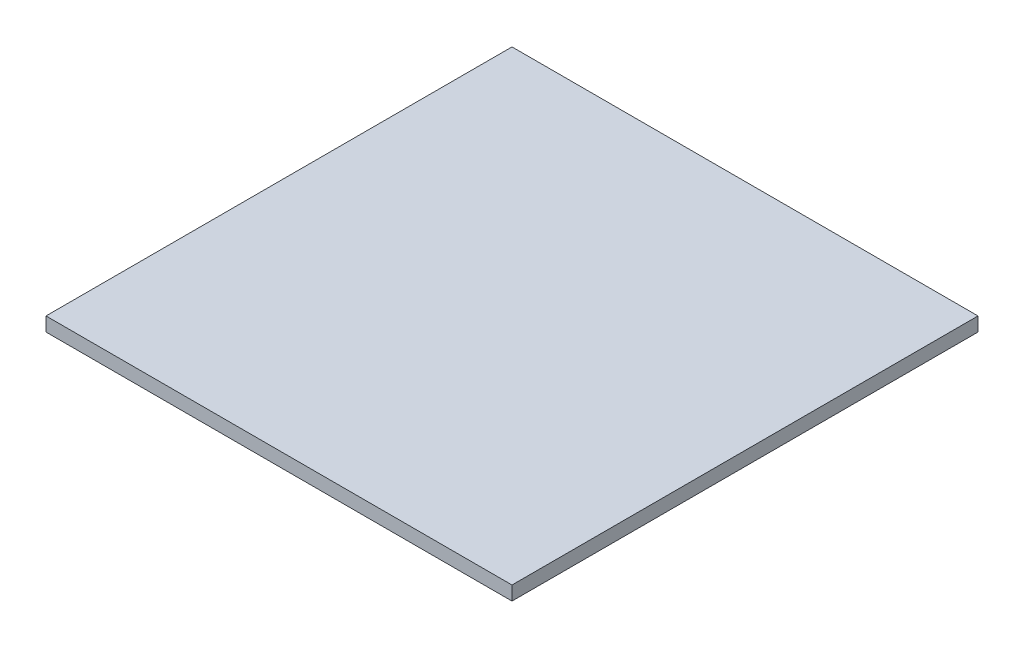
SolidWorks part; units mm, degrees
ref_plane "Front Plane" through (0, 0, 0) normal (0, 0, 1) x (1, 0, 0)
ref_plane "Top Plane" through (0, 0, 0) normal (0, 1, 0) x (1, 0, 0)
ref_plane "Right Plane" through (0, 0, 0) normal (1, 0, 0) x (0, 0, -1)
sketch "Sketch1" plane through (0, 0, 0) normal (0, 1, 0) x (1, 0, 0)
  line L0 (-29.6545, 29.6545) -> (29.6545, 29.6545)
  line L1 (-30.2895, -30.2895) -> (30.2895, -30.2895) construction
  line L2 (-30.2895, -30.2895) -> (-30.2895, 30.2895) construction
  line L3 (-30.2895, 30.2895) -> (30.2895, 30.2895) construction
  line L4 (30.2895, -30.2895) -> (30.2895, 30.2895) construction
  line L5 (-30.2895, -30.2895) -> (30.2895, 30.2895) construction
  line L6 (-30.2895, 30.2895) -> (30.2895, -30.2895) construction
  line L7 (29.6545, -29.6545) -> (29.6545, 29.6545)
  line L8 (-29.6545, -29.6545) -> (29.6545, -29.6545)
  line L9 (-29.6545, -29.6545) -> (-29.6545, 29.6545)
  point P0 (0, 0)
  dimension "D1" = 60.579
  dimension "D2" = 60.579
  dimension "D3" = 0.635
extrude "Boss-Extrude1" add sketch "Sketch1" along normal blind 1.778
